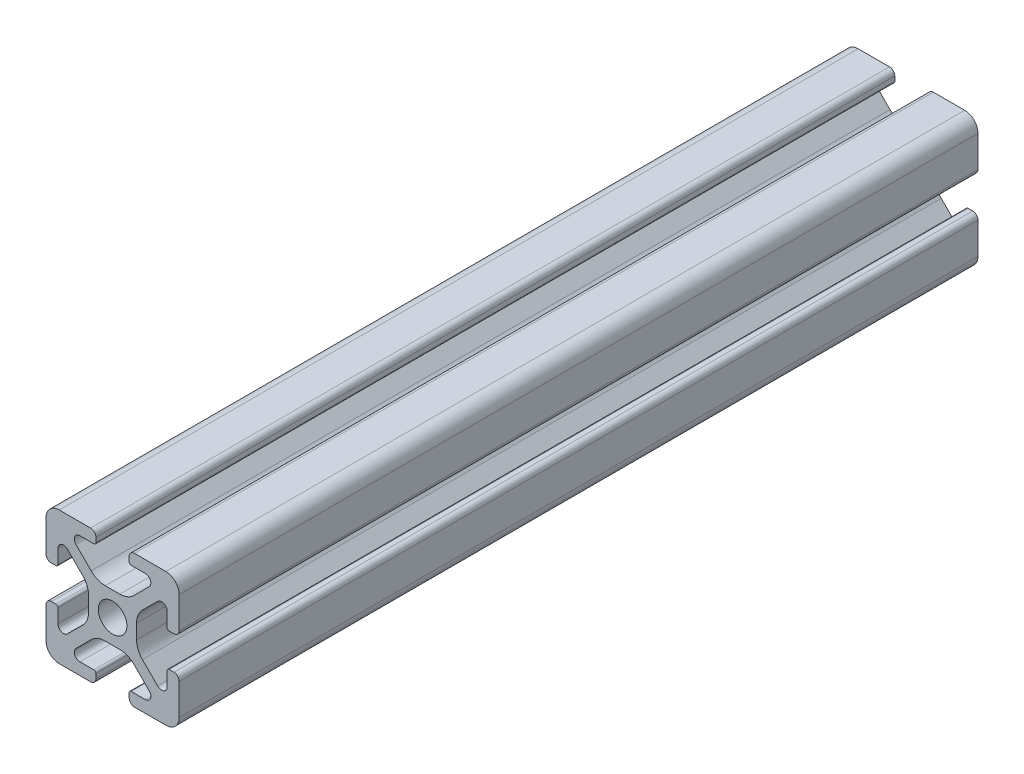
SolidWorks part; units mm, degrees
ref_plane "Front Plane" through (0, 0, 0) normal (0, 0, 1) x (1, 0, 0)
ref_plane "Top Plane" through (0, 0, 0) normal (0, 1, 0) x (1, 0, 0)
ref_plane "Right Plane" through (0, 0, 0) normal (1, 0, 0) x (0, 0, -1)
sketch "Sketch1" plane through (0, 0, 0) normal (0, 0, 1) x (1, 0, 0)
  line L0 (0, 10) -> (0, -10) construction
  line L1 (10, 0) -> (-10, 0) construction
  line L2 (-2.5, 10) -> (2.5, 10) construction
  line L3 (-5.75, 8.2) -> (5.75, 8.2) construction
  circle A0 centre (0, 0) radius 2.15 construction
  point P4 (0, 0)
  point P8 (0, 0)
  point P10 (0, 3.6)
  point P14 (0, 10)
  point P17 (0, 8.2)
  dimension "Thru Hole" = 4.3
  dimension "Height" = 20
  dimension "T Slot Depth" = 6.4
  dimension "T Slot Top Width" = 5
  dimension "T Slot Max Width" = 11.5
  dimension "Wall" = 1.8
sketch "Sketch2" plane through (0, 0, 0) normal (1, 0, 0) x (0, 0, -1)
  line L0 (152.4, 0) -> (-152.4, 0) construction
  point P4 (0, 0)
  dimension "D1" = 304.8
sketch "Sketch3" plane through (0, 0, 0) normal (0, 0, 1) x (1, 0, 0)
  line L0 (3.2874, 10) -> (8, 10)
  line L1 (10, 8) -> (10, -8) construction
  line L2 (8, -10) -> (-8, -10) construction
  line L3 (-10, 10) -> (10, -10) construction
  line L4 (2.5, 9.2126) -> (2.5, 8.5048)
  line L5 (-5.75, 8.2) -> (5.75, 8.2) construction
  line L6 (2.8048, 8.2) -> (4.9118, 8.2)
  line L7 (5.5045, 6.7691) -> (3.2141, 4.4787)
  line L8 (1.0928, 3.6) -> (-1.0928, 3.6)
  line L9 (0, 10) -> (0, -10) construction
  line L10 (5.75, 8.2) -> (5.75, 0) construction
  line L11 (10, 0) -> (-10, 0) construction
  line L12 (0, 0) -> (0, 10) construction
  line L13 (-2.5, 9.2126) -> (-2.5, 8.5048)
  line L14 (-5.5045, 6.7691) -> (-3.2141, 4.4787)
  line L15 (-2.8048, 8.2) -> (-4.9118, 8.2)
  line L16 (-3.2874, 10) -> (-8, 10)
  line L17 (0, 0) -> (-10, 0) construction
  line L18 (-10, 3.2874) -> (-10, 8)
  line L19 (-8.2, 2.8048) -> (-8.2, 4.9118)
  line L20 (-6.7691, 5.5045) -> (-4.4787, 3.2141)
  line L21 (-9.2126, 2.5) -> (-8.5048, 2.5)
  line L22 (-3.6, -1.0928) -> (-3.6, 1.0928)
  line L23 (-6.7691, -5.5045) -> (-4.4787, -3.2141)
  line L24 (-8.2, -2.8048) -> (-8.2, -4.9118)
  line L25 (-9.2126, -2.5) -> (-8.5048, -2.5)
  line L26 (-10, -3.2874) -> (-10, -8)
  line L27 (9.2126, -2.5) -> (8.5048, -2.5)
  line L28 (8.2, -2.8048) -> (8.2, -4.9118)
  line L29 (6.7691, -5.5045) -> (4.4787, -3.2141)
  line L30 (3.6, -1.0928) -> (3.6, 1.0928)
  line L31 (9.2126, 2.5) -> (8.5048, 2.5)
  line L32 (6.7691, 5.5045) -> (4.4787, 3.2141)
  line L33 (8.2, 2.8048) -> (8.2, 4.9118)
  line L34 (10, 8) -> (10, 3.2874)
  line L35 (10, -3.2874) -> (10, -8)
  line L36 (3.2874, -10) -> (8, -10)
  line L37 (-3.2874, -10) -> (-8, -10)
  line L38 (-6.7691, -5.5045) -> (-4.4787, -3.2141)
  line L39 (-2.8048, -8.2) -> (-4.9118, -8.2)
  line L40 (-5.5045, -6.7691) -> (-3.2141, -4.4787)
  line L41 (-2.5, -9.2126) -> (-2.5, -8.5048)
  line L42 (1.0928, -3.6) -> (-1.0928, -3.6)
  line L43 (5.5045, -6.7691) -> (3.2141, -4.4787)
  line L44 (2.8048, -8.2) -> (4.9118, -8.2)
  line L45 (2.5, -9.2126) -> (2.5, -8.5048)
  arc A0 (4.9118, 8.2) -> (5.5045, 6.7691) centre (4.9118, 7.3618) cw
  arc A1 (3.2141, 4.4787) -> (1.0928, 3.6) centre (1.0928, 6.6) cw
  circle A2 centre (0, 0) radius 2.15 construction
  circle A3 centre (0, 0) radius 2.15
  arc A4 (3.2874, 10) -> (2.5, 9.2126) centre (3.2874, 9.2126) ccw
  arc A5 (2.5, 8.5048) -> (2.8048, 8.2) centre (2.8048, 8.5048) ccw
  arc A6 (-3.2874, 10) -> (-2.5, 9.2126) centre (-3.2874, 9.2126) cw
  arc A7 (-4.9118, 8.2) -> (-5.5045, 6.7691) centre (-4.9118, 7.3618) ccw
  arc A8 (-3.2141, 4.4787) -> (-1.0928, 3.6) centre (-1.0928, 6.6) ccw
  arc A9 (-2.5, 8.5048) -> (-2.8048, 8.2) centre (-2.8048, 8.5048) cw
  arc A10 (-8.5048, 2.5) -> (-8.2, 2.8048) centre (-8.5048, 2.8048) ccw
  arc A11 (-4.4787, 3.2141) -> (-3.6, 1.0928) centre (-6.6, 1.0928) cw
  arc A12 (-8.2, 4.9118) -> (-6.7691, 5.5045) centre (-7.3618, 4.9118) cw
  arc A13 (-10, 3.2874) -> (-9.2126, 2.5) centre (-9.2126, 3.2874) ccw
  arc A14 (-8.5048, -2.5) -> (-8.2, -2.8048) centre (-8.5048, -2.8048) cw
  arc A15 (-10, -3.2874) -> (-9.2126, -2.5) centre (-9.2126, -3.2874) cw
  arc A16 (-4.4787, -3.2141) -> (-3.6, -1.0928) centre (-6.6, -1.0928) ccw
  arc A17 (-8.2, -4.9118) -> (-6.7691, -5.5045) centre (-7.3618, -4.9118) ccw
  arc A26 (-8, -10) -> (-10, -8) centre (-8, -8) cw
  arc A27 (-8, 10) -> (-10, 8) centre (-8, 8) ccw
  arc A28 (8, 10) -> (10, 8) centre (8, 8) cw
  arc A29 (10, -8) -> (8, -10) centre (8, -8) cw
  arc A30 (8.2, -4.9118) -> (6.7691, -5.5045) centre (7.3618, -4.9118) cw
  arc A31 (4.4787, -3.2141) -> (3.6, -1.0928) centre (6.6, -1.0928) cw
  arc A32 (10, -3.2874) -> (9.2126, -2.5) centre (9.2126, -3.2874) ccw
  arc A33 (8.5048, -2.5) -> (8.2, -2.8048) centre (8.5048, -2.8048) ccw
  arc A34 (10, 3.2874) -> (9.2126, 2.5) centre (9.2126, 3.2874) cw
  arc A35 (8.2, 4.9118) -> (6.7691, 5.5045) centre (7.3618, 4.9118) ccw
  arc A36 (4.4787, 3.2141) -> (3.6, 1.0928) centre (6.6, 1.0928) ccw
  arc A37 (8.5048, 2.5) -> (8.2, 2.8048) centre (8.5048, 2.8048) cw
  arc A38 (-2.5, -8.5048) -> (-2.8048, -8.2) centre (-2.8048, -8.5048) ccw
  arc A39 (-3.2141, -4.4787) -> (-1.0928, -3.6) centre (-1.0928, -6.6) cw
  arc A40 (-4.9118, -8.2) -> (-5.5045, -6.7691) centre (-4.9118, -7.3618) cw
  arc A41 (-3.2874, -10) -> (-2.5, -9.2126) centre (-3.2874, -9.2126) ccw
  arc A42 (2.5, -8.5048) -> (2.8048, -8.2) centre (2.8048, -8.5048) cw
  arc A43 (3.2874, -10) -> (2.5, -9.2126) centre (3.2874, -9.2126) cw
  arc A44 (3.2141, -4.4787) -> (1.0928, -3.6) centre (1.0928, -6.6) ccw
  arc A45 (4.9118, -8.2) -> (5.5045, -6.7691) centre (4.9118, -7.3618) ccw
  point P36 (2.5, 10)
  point P39 (2.5, 8.2)
  point P49 (0, 3.6)
  point P77 (-3.6, 0)
  point P78 (-8.2, -2.5)
  point P79 (-10, -2.5)
  point P104 (-10, -10)
  point P110 (10, 10)
  point P114 (10, -2.5)
  point P115 (8.2, -2.5)
  point P116 (3.6, 0)
  point P141 (0, -3.6)
  dimension "D1" = 3
  dimension "D2" = 0.8382
  dimension "D4" = 0.7874
  dimension "D5" = 0.3048
  dimension "D6" = 2
  dimension "D3" = 45
extrude "Boss-Extrude1" add sketch "Sketch3" along normal blind 120 contours A45 L44 A42 L45 A43 L36 A29 L35 A32 L27 A33 L28 A30 L29 A31 L30 A36 L32 A35 L33 A37 L31 A34 L34 A28 L0 A4 L4 A5 L6 A0 L7 A1 L8 A8 L14 A7 L15 A9 L13 A6 L16 A27 L18 A13 L21 A10 L19 A12 L20 A11
